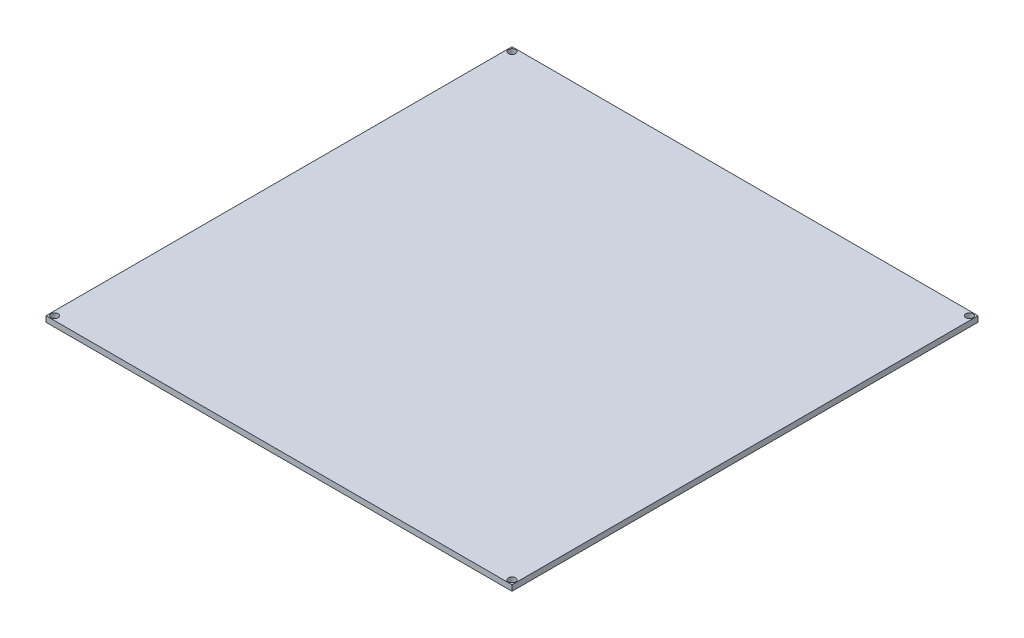
SolidWorks part; units mm, degrees
ref_plane "Front Plane" through (0, 0, 0) normal (0, 0, 1) x (1, 0, 0)
ref_plane "Top Plane" through (0, 0, 0) normal (0, 1, 0) x (1, 0, 0)
ref_plane "Right Plane" through (0, 0, 0) normal (1, 0, 0) x (0, 0, -1)
sketch "Sketch1" plane through (0, 0, 0) normal (0, 1, 0) x (1, 0, 0)
  line L1 (-176, 98.8696) -> (151, 98.8696)
  line L2 (-176, 98.8696) -> (-176, -228.1304)
  line L3 (-176, -228.1304) -> (151, -228.1304)
  line L4 (151, 98.8696) -> (151, -228.1304)
  circle A0 centre (-173, -225.1304) radius 2.5
  circle A1 centre (-173, 95.8696) radius 2.5
  circle A2 centre (148, 95.8696) radius 2.5
  circle A3 centre (148, -225.1304) radius 2.5
  dimension "D3" = 3
  dimension "D5" = 3
  dimension "D1" = 327
  dimension "D2" = 327
  dimension "D4" = 3
  dimension "D6" = 3
  dimension "D7" = 3
  dimension "D8" = 3
  dimension "D9" = 3
  dimension "D10" = 3
extrude "Boss-Extrude1" add sketch "Sketch1" along normal blind 4
